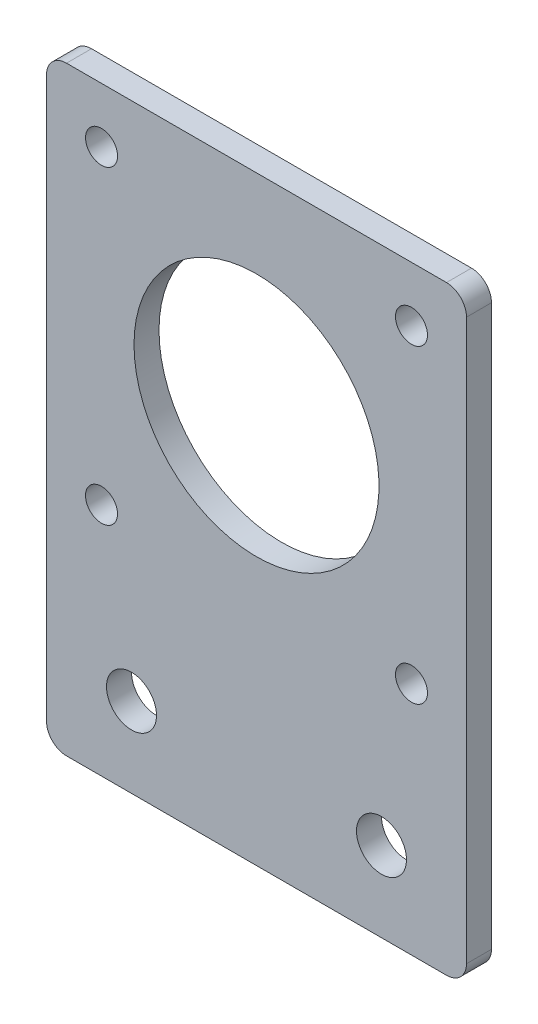
SolidWorks part; units mm, degrees
ref_plane "Front Plane" through (0, 0, 0) normal (0, 0, 1) x (1, 0, 0)
ref_plane "Top Plane" through (0, 0, 0) normal (0, 1, 0) x (1, 0, 0)
ref_plane "Right Plane" through (0, 0, 0) normal (1, 0, 0) x (0, 0, -1)
ref_plane "Plane1" through (0, 0, 1.25) normal (0, 0, 1) x (1, 0, 0)
sketch "Sketch1" plane through (0, 0, 1.25) normal (0, 0, 1) x (1, 0, 0)
  line L0 (-21, 19) -> (-21, -37)
  line L1 (-19, -39) -> (19, -39)
  line L2 (21, -37) -> (21, 19)
  line L3 (19, 21) -> (-19, 21)
  circle A0 centre (-12.5, -31) radius 2.5
  circle A1 centre (-15.5, 15.5) radius 1.6
  circle A2 centre (15.5, -15.5) radius 1.6
  arc A3 (-21, -37) -> (-19, -39) centre (-19, -37) ccw
  arc A4 (19, -39) -> (21, -37) centre (19, -37) ccw
  arc A5 (21, 19) -> (19, 21) centre (19, 19) ccw
  arc A6 (-19, 21) -> (-21, 19) centre (-19, 19) ccw
  circle A7 centre (0, 0) radius 12.25
  circle A8 centre (-15.5, -15.5) radius 1.6
  circle A9 centre (15.5, 15.5) radius 1.6
  circle A10 centre (12.5, -31) radius 2.5
extrude "Boss-Extrude1" add sketch "Sketch1" against normal blind 2.5
